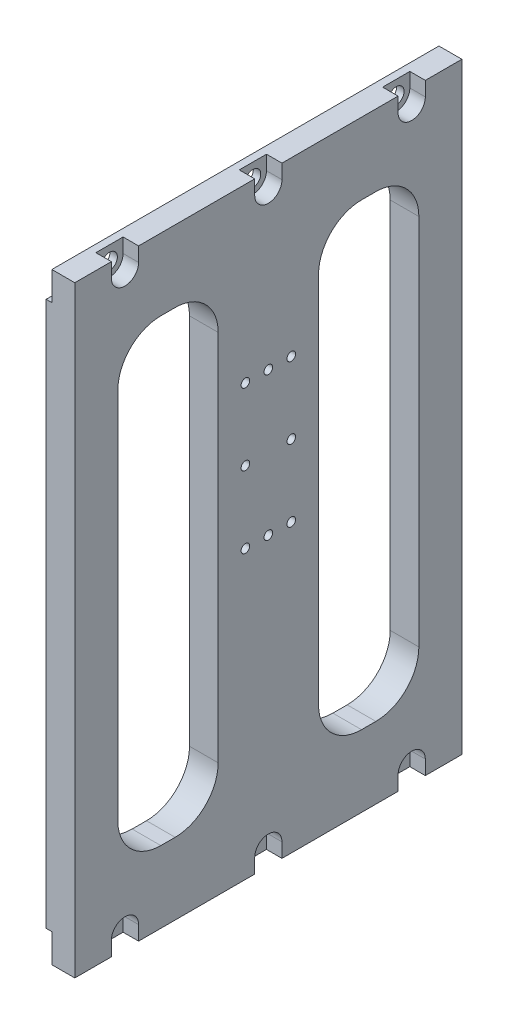
SolidWorks part; units mm, degrees
ref_plane "Front" through (0, 0, 0) normal (0, 0, 1) x (1, 0, 0)
ref_plane "Top" through (0, 0, 0) normal (0, 1, 0) x (1, 0, 0)
ref_plane "Right" through (0, 0, 0) normal (1, 0, 0) x (0, 0, -1)
sketch "Sketch1" plane through (0, 0, 0) normal (1, 0, 0) x (0, 0, -1)
  line L2 (0, 210) -> (135, 210)
  line L3 (0, 210) -> (0, 0)
  line L4 (0, 0) -> (135, 0)
  line L5 (135, 210) -> (135, 0)
  dimension "D1" = 210
  dimension "D2" = 135
extrude "Boss-Extrude1" add sketch "Sketch1" along normal blind 10
sketch "Sketch4" plane through (10, 0, 0) normal (1, 0, 0) x (0, 0, -1)
  line L0 (135, 0) -> (135, 210) construction
  line L1 (0, 0) -> (135, 0)
  line L2 (0, 0) -> (0, 10)
  line L3 (0, 10) -> (135, 10)
  line L4 (135, 0) -> (135, 10)
  line L5 (135, 0) -> (135, 210) construction
  line L6 (0, 210) -> (135, 210)
  line L7 (0, 210) -> (0, 200)
  line L8 (0, 200) -> (135, 200)
  line L9 (135, 210) -> (135, 200)
  dimension "D1" = 10
  dimension "D2" = 190
extrude "Cut-Extrude1" cut sketch "Sketch4" against normal through all from offset 8
sketch "Sketch15" plane through (10, 0, 0) normal (1, 0, 0) x (0, 0, -1)
  line L1 (15, 185) -> (50, 185)
  line L2 (15, 185) -> (15, 25)
  line L3 (15, 25) -> (50, 25)
  line L4 (50, 185) -> (50, 25)
  line L5 (85, 185) -> (120, 185)
  line L6 (85, 185) -> (85, 25)
  line L7 (85, 25) -> (120, 25)
  line L8 (120, 185) -> (120, 25)
  dimension "D1" = 35
  dimension "D2" = 35
  dimension "D3" = 15
  dimension "D4" = 25
  dimension "D5" = 160
extrude "Cut-Extrude2" cut sketch "Sketch15" against normal through all
sketch "Sketch16" plane through (10, 0, 0) normal (1, 0, 0) x (0, 0, -1)
  circle A0 centre (67.5, 100) radius 1.5
  circle A1 centre (67.5, 150) radius 1.5
  dimension "D1" = 3
  dimension "D2" = 67.5
  dimension "D3" = 100
  dimension "D4" = 50
extrude "Cut-Extrude3" cut sketch "Sketch16" against normal blind 5
sketch "Sketch6" plane through (10, 0, 0) normal (-1, 0, 0) x (0, 0, 1)
  line L0 (-22.25, 5) -> (-22.25, 0)
  line L1 (-12.75, 5) -> (-12.75, 0)
  line L2 (-22.25, 0) -> (-12.75, 0)
  line L3 (0, 0) -> (-135, 0) construction
  line L4 (-22.25, 205) -> (-22.25, 210)
  line L5 (-12.75, 205) -> (-12.75, 210)
  line L6 (-22.25, 210) -> (-12.75, 210)
  line L7 (-135, 210) -> (0, 210) construction
  arc A0 (-12.75, 5) -> (-22.25, 5) centre (-17.5, 5) ccw
  arc A1 (-22.25, 205) -> (-12.75, 205) centre (-17.5, 205) ccw
  dimension "D1" = 9.5
  dimension "D2" = 5
  dimension "D3" = 17.5
  dimension "D4" = 205
extrude "Cut-Extrude4" cut sketch "Sketch6" along normal blind 5.4
hole_wizard "Ø3.0 (3) Diameter Hole1" positions "Sketch18" profile "Sketch17" hole size "Ø3.0" standard "JIS" end condition through all
sketch "Sketch18" plane through (10, 0, 0) normal (1, 0, 0) x (0, 0, -1)
  point P0 (59.5, 100)
  dimension "D1" = 59.5
  dimension "D2" = 100
sketch "Sketch17" plane through (10, 100, -59.5) normal (0, 1, 0) x (0, 0, -1)
  line L0 (0, 0) -> (0, 10)
  line L1 (0, 10) -> (1.5, 10)
  line L2 (1.5, 10) -> (1.5, 0)
  line L5 (1.5, 0) -> (0, 0)
  line L11 (0, -6.35) -> (0, 107.95) construction
  dimension "Thru Hole Dia." = 3
  dimension "Thru Hole Depth" = 10
pattern_linear "LPattern4" count 2 spacing 16 along (0, 0, -1) count 3 spacing 25 along (0, 1, 0) of "Ø3.0 (3) Diameter Hole1"
pattern_linear "LPattern1" count 3 spacing 50 along (0, 0, -1) of "Cut-Extrude4"
hole_wizard "Ø5.5 (5.5) Diameter Hole1" positions "Sketch14" profile "Sketch13" hole size "Ø5.5" standard "JIS" end condition through all
sketch "Sketch14" plane through (4.6, 0, 0) normal (1, 0, 0) x (0, 0, -1)
  point P0 (17.5, 205)
  point P17 (17.5, 5)
sketch "Sketch13" plane through (4.6, 205, -17.5) normal (0, 1, 0) x (0, 0, -1)
  line L0 (0, 0) -> (0, 4.6)
  line L1 (0, 4.6) -> (2.75, 4.6)
  line L2 (2.75, 4.6) -> (2.75, 0)
  line L5 (2.75, 0) -> (0, 0)
  line L11 (0, -6.35) -> (0, 107.95) construction
  dimension "Thru Hole Dia." = 5.5
  dimension "Thru Hole Depth" = 4.6
pattern_linear "LPattern3" count 3 spacing 50 along (0, 0, -1) of "Ø5.5 (5.5) Diameter Hole1"
fillet "Fillet1" radius 15 8 edges at (5, 185, -85) (5, 185, -120) (5, 25, -120) (5, 25, -85) (5, 185, -15) (5, 185, -50) (5, 25, -50) (5, 25, -15)
